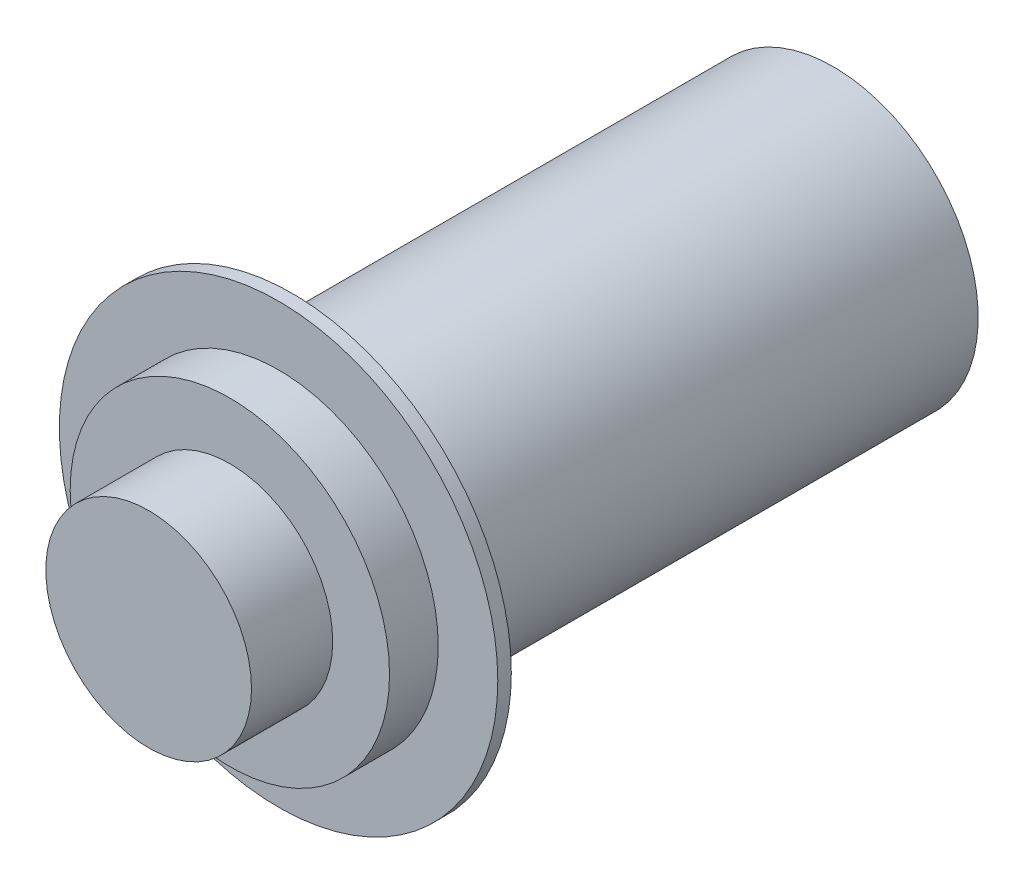
SolidWorks part; units mm, degrees
ref_plane "Plan de face" through (0, 0, 0) normal (0, 0, 1) x (1, 0, 0)
ref_plane "Plan de dessus" through (0, 0, 0) normal (0, 1, 0) x (1, 0, 0)
ref_plane "Plan de droite" through (0, 0, 0) normal (1, 0, 0) x (0, 0, -1)
sketch "Esquisse1" plane through (0, 0, 0) normal (0, 0, 1) x (1, 0, 0)
  circle A0 centre (0, 0) radius 8.1
  dimension "D1" = 16.2
extrude "Boss.-Extru.1" add sketch "Esquisse1" along normal blind 0.5
sketch "Esquisse2" plane through (0, 0, 0.5) normal (0, 0, 1) x (1, 0, 0)
  circle A0 centre (0, 0) radius 5.9
  dimension "D1" = 11.8
extrude "Boss.-Extru.2" add sketch "Esquisse2" along normal blind 1.8
sketch "Esquisse3" plane through (0, 0, 2.3) normal (0, 0, 1) x (1, 0, 0)
  circle A0 centre (0, 0) radius 3.8
  dimension "D1" = 7.6
extrude "Boss.-Extru.3" add sketch "Esquisse3" along normal blind 3
sketch "Esquisse4" plane through (0, 0, 0) normal (0, 0, -1) x (-1, 0, 0)
  circle A0 centre (0, 0) radius 5.35
  dimension "D1" = 10.7
extrude "Boss.-Extru.4" add sketch "Esquisse4" along normal blind 20
